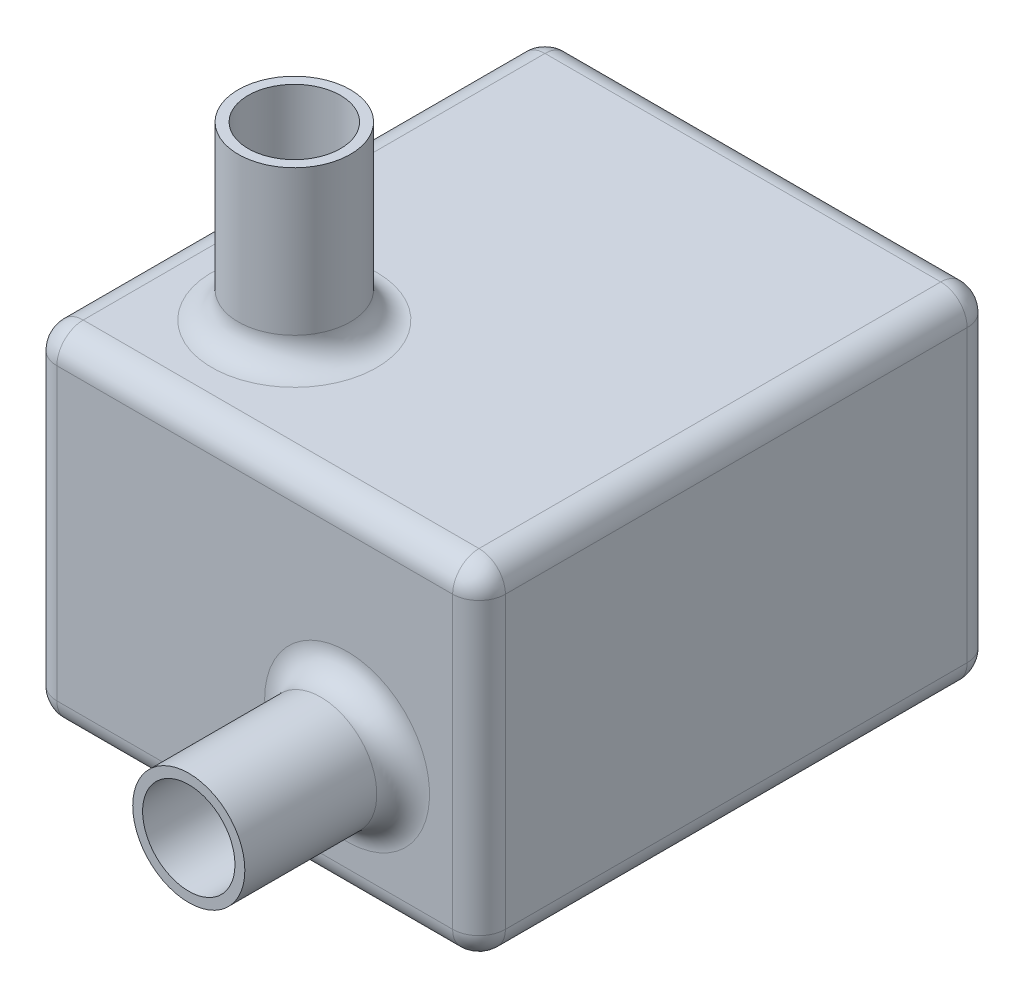
SolidWorks part; units mm, degrees
ref_plane "Front Plane" through (0, 0, 0) normal (0, 0, 1) x (1, 0, 0)
ref_plane "Top Plane" through (0, 0, 0) normal (0, 1, 0) x (1, 0, 0)
ref_plane "Right Plane" through (0, 0, 0) normal (1, 0, 0) x (0, 0, -1)
sketch "Sketch1" plane through (0, 0, 0) normal (0, 1, 0) x (1, 0, 0)
  line L1 (-17, -19.5) -> (17, -19.5)
  line L2 (-17, -19.5) -> (-17, 19.5)
  line L3 (-17, 19.5) -> (17, 19.5)
  line L4 (17, -19.5) -> (17, 19.5)
  line L5 (-17, -19.5) -> (17, 19.5) construction
  line L6 (-17, 19.5) -> (17, -19.5) construction
  point P0 (0, 0)
  dimension "D1" = 34
  dimension "D2" = 39
extrude "Boss-Extrude1" add sketch "Sketch1" along normal blind 26
sketch "Sketch2" plane through (0, 26, 0) normal (0, 1, 0) x (1, 0, 0)
  line L0 (-17, -19.5) -> (-7, -19.5)
  line L1 (-17, -19.5) -> (17, -19.5) construction
  line L2 (-7, -19.5) -> (-7, -9.5)
  circle A0 centre (-7, -9.5) radius 4.25
  circle A1 centre (-7, -9.5) radius 3.5
  dimension "D3" = 8.5
  dimension "D4" = 7
  dimension "D1" = 10
  dimension "D2" = 10
extrude "Boss-Extrude2" add sketch "Sketch2" along normal blind 13
sketch "Sketch3" plane through (0, 0, 19.5) normal (0, 0, 1) x (1, 0, 0)
  line L0 (17, 0) -> (7, 0)
  line L1 (-17, 0) -> (17, 0) construction
  line L2 (7, 0) -> (7, 10)
  circle A0 centre (7, 10) radius 4.25
  circle A1 centre (7, 10) radius 3.5
  dimension "D3" = 8.5
  dimension "D4" = 7
  dimension "D1" = 10
  dimension "D2" = 10
extrude "Boss-Extrude4" add sketch "Sketch3" along normal blind 12
fillet "Fillet1" radius 2 12 edges at (0, 26, 19.5) (0, 0, -19.5) (17, 13, -19.5) (0, 26, -19.5) (-17, 13, -19.5) (-17, 0, 0) (-17, 26, 0) (17, 0, 0) (17, 26, 0) (-17, 13, 19.5) (0, 0, 19.5) (17, 13, 19.5)
fillet "Fillet3" radius 2 2 edges at (2.75, 10, 19.5) (-7, 26, 5.25)
equation "\"ML\"=34"
equation "\"D1@Sketch1\"=\"ML\""
equation "\"MH\"= 26"
equation "\"D1@Boss-Extrude1\"=\"MH\""
equation "\"OFF2\"=10"
equation "\"D2@Sketch2\"=\"OFF2\""
equation "\"OFF1\"=10"
equation "\"D1@Sketch2\"=\"OFF1\""
equation "\"D2@Sketch3\"=\"OFF1\""
equation "\"D1@Sketch3\"=\"OFF2\" "
equation "\"OUTOD\"= 8.5"
equation "\"D3@Sketch3\"=\"OUTOD\""
equation "\"D3@Sketch2\"=\"OUTOD\""
equation "\"OUTH\"=13"
equation "\"D1@Boss-Extrude2\"=\"OUTH\""
equation "\"OUTID\"= 7"
equation "\"D4@Sketch3\"=\"OUTID\""
equation "\"D2@Sketch1\"=39"
equation "\"D4@Sketch2\"=\"OUTID\""
equation "\"F\"=2"
equation "\"D1@Fillet1\"=\"F\""
equation "\"F2\"=2"
equation "\"OUTH2\"=12"
equation "\"D1@Boss-Extrude4\"=\"OUTH2\""
equation "\"D1@Fillet3\"=\"F2\""
equation "\"HOLED\"=5"
equation "\"D1@Sketch5\"=\"HOLED\""
equation "\"D3@Sketch5\"=2+0.5*\"HOLED\""
